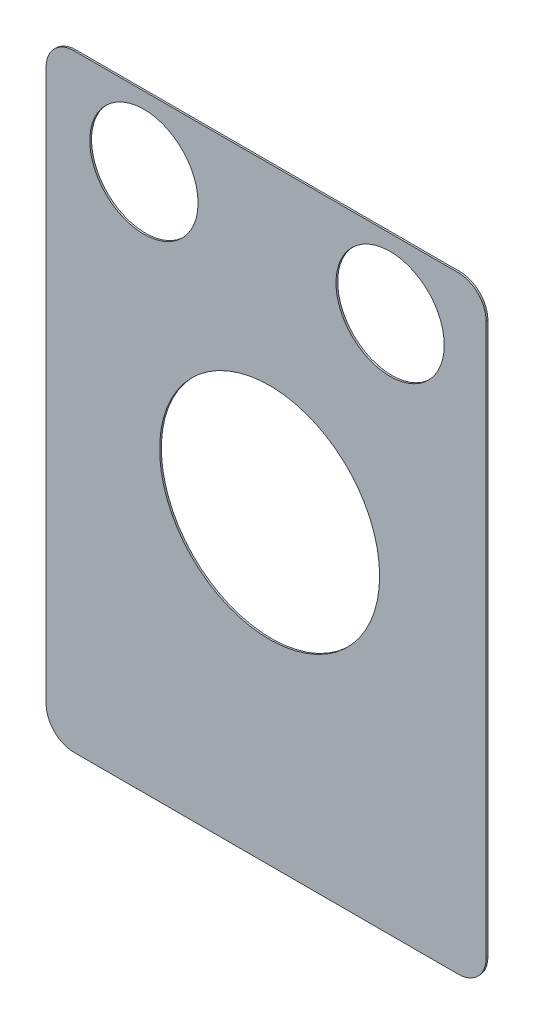
SolidWorks part; units mm, degrees
material "Nickel"
ref_plane "Front Plane" through (0, 0, 0) normal (0, 0, 1) x (1, 0, 0)
ref_plane "Top Plane" through (0, 0, 0) normal (0, 1, 0) x (1, 0, 0)
ref_plane "Right Plane" through (0, 0, 0) normal (1, 0, 0) x (0, 0, -1)
sketch "Sketch1" plane through (0, 0, 0) normal (0, 0, 1) x (1, 0, 0)
  line L1 (-27.94, -44.196) -> (27.94, -44.196)
  line L2 (-32.004, -40.132) -> (-32.004, 40.132)
  line L3 (-27.94, 44.196) -> (27.94, 44.196)
  line L4 (32.004, -40.132) -> (32.004, 40.132)
  line L5 (-32.004, -44.196) -> (32.004, 44.196) construction
  line L6 (-32.004, 44.196) -> (32.004, -44.196) construction
  arc A0 (-32.004, -40.132) -> (-27.94, -44.196) centre (-27.94, -40.132) ccw
  arc A1 (27.94, -44.196) -> (32.004, -40.132) centre (27.94, -40.132) ccw
  arc A2 (32.004, 40.132) -> (27.94, 44.196) centre (27.94, 40.132) ccw
  arc A3 (-27.94, 44.196) -> (-32.004, 40.132) centre (-27.94, 40.132) ccw
  point P0 (0, 0)
  dimension "D3" = 4.064
  dimension "D1" = 64.008
  dimension "D2" = 88.392
extrude "Boss-Extrude1" add sketch "Sketch1" against normal blind 0.254
sketch "Sketch2" plane through (0, 0, 0) normal (0, 0, 1) x (1, 0, 0)
  line L0 (27.94, 44.196) -> (-27.94, 44.196) construction
  line L2 (32.004, -40.132) -> (32.004, 40.132) construction
  circle A0 centre (18.034, 34.036) radius 7.874
  circle A1 centre (-17.78, 34.036) radius 7.874
  dimension "D1" = 15.748
  dimension "D3" = 35.814
  dimension "D4" = 10.16
  dimension "D5" = 13.97
extrude "Cut-Extrude1" cut sketch "Sketch2" against normal blind 0.254
sketch "Sketch3" plane through (0, 0, 0) normal (0, 0, 1) x (1, 0, 0)
  line L0 (-32.004, 40.132) -> (-32.004, -40.132) construction
  line L1 (-27.94, -44.196) -> (27.94, -44.196) construction
  circle A0 centre (0.508, 0.254) radius 16.002
  dimension "D1" = 32.004
  dimension "D2" = 32.512
  dimension "D3" = 44.45
extrude "Cut-Extrude2" cut sketch "Sketch3" against normal blind 0.254
